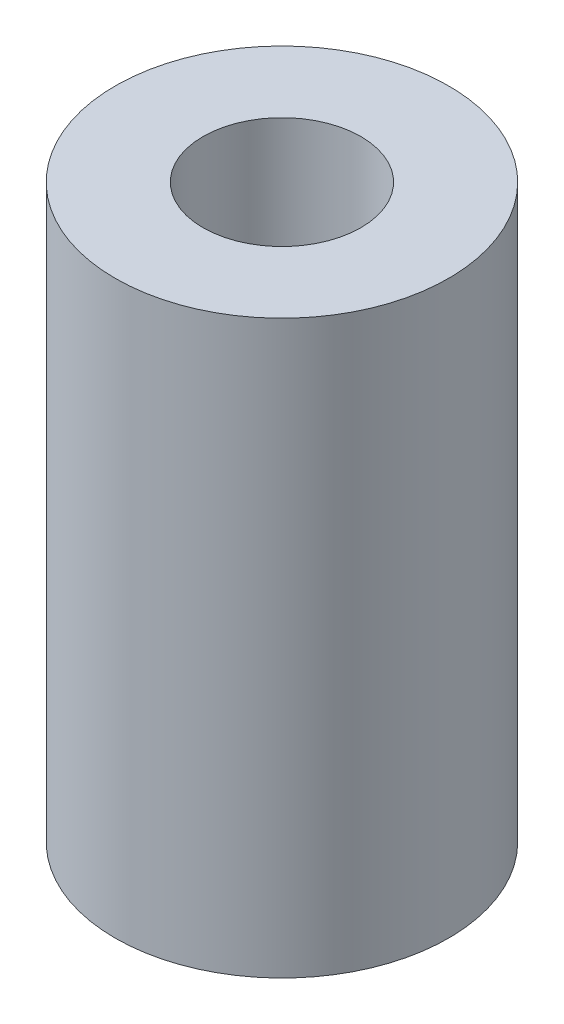
SolidWorks part; units mm, degrees
ref_plane "Front Plane" through (0, 0, 0) normal (0, 0, 1) x (1, 0, 0)
ref_plane "Top Plane" through (0, 0, 0) normal (0, 1, 0) x (1, 0, 0)
ref_plane "Right Plane" through (0, 0, 0) normal (1, 0, 0) x (0, 0, -1)
sketch "Sketch1" plane through (0, 0, 0) normal (0, 1, 0) x (1, 0, 0)
  circle A0 centre (0, 0) radius 1.8
  circle A1 centre (0, 0) radius 3.8
  dimension "D1" = 3.6
  dimension "D2" = 2
extrude "Boss-Extrude1" add sketch "Sketch1" along normal blind 13.025
